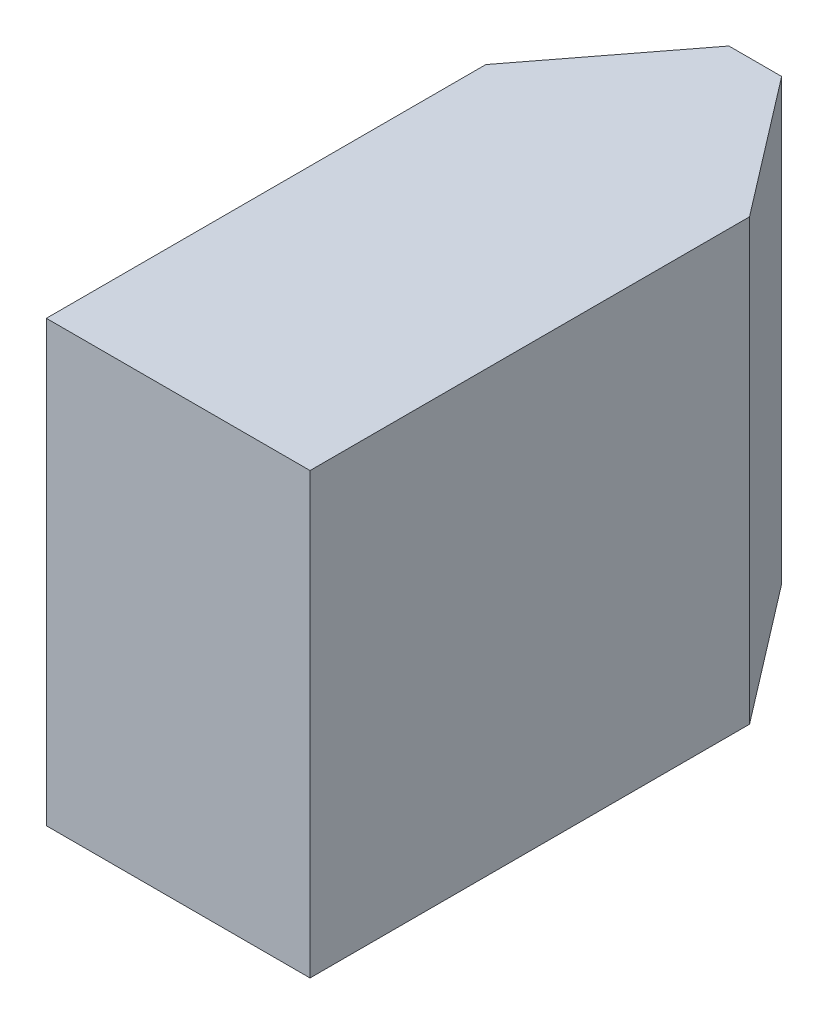
SolidWorks part; units mm, degrees
ref_plane "Спереди" through (0, 0, 0) normal (0, 0, 1) x (1, 0, 0)
ref_plane "Сверху" through (0, 0, 0) normal (0, 1, 0) x (1, 0, 0)
ref_plane "Справа" through (0, 0, 0) normal (1, 0, 0) x (0, 0, -1)
sketch "Эскиз1" plane through (0, 0, 0) normal (0, 1, 0) x (1, 0, 0)
  line L0 (-15, 50) -> (-3, 65.656)
  line L1 (-15, 0) -> (15, 0)
  line L2 (-15, 0) -> (-15, 50)
  line L4 (15, 0) -> (15, 50)
  line L5 (-3, 65.656) -> (3, 65.656)
  line L6 (3, 65.656) -> (15, 50)
  point P4 (0, 0)
  point P6 (0, 65.656)
  point P8 (-15, 50.2693)
  point P10 (0, 0)
  point P11 (0, 0)
  point P12 (0, 0)
extrude "Бобышка-Вытянуть1" add sketch "Эскиз1" along normal blind 50
